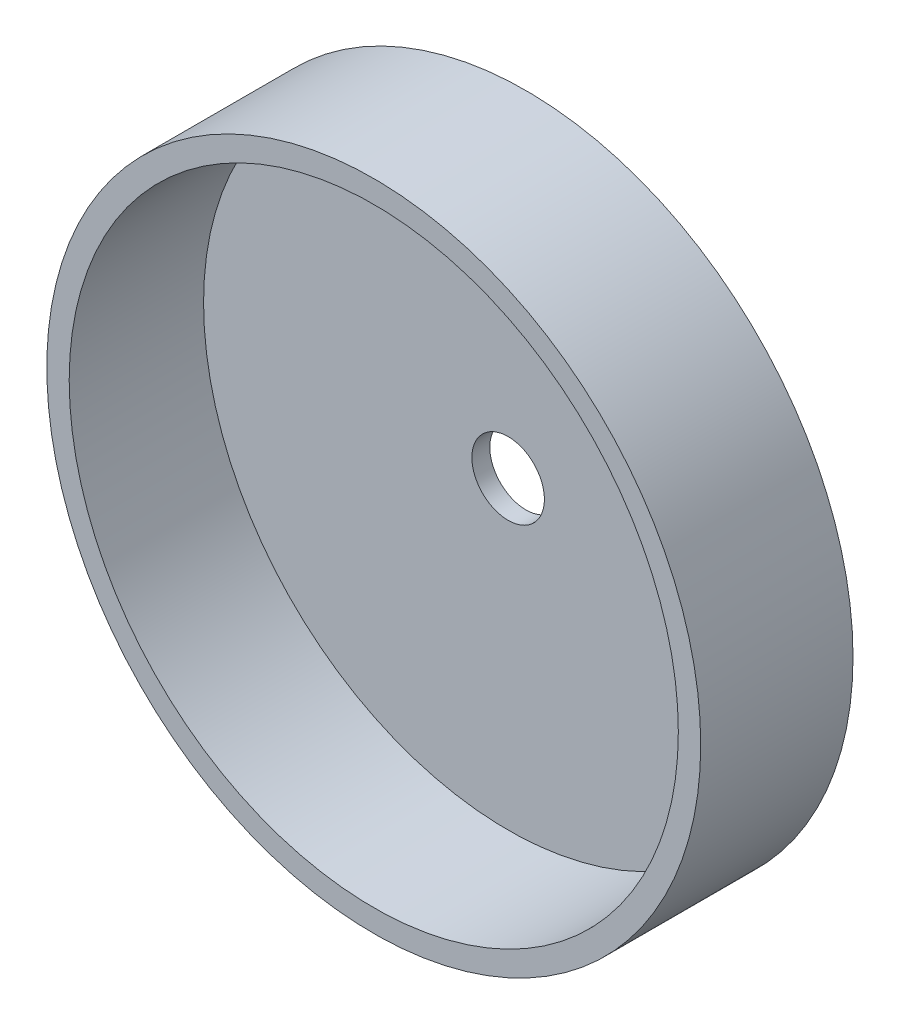
SolidWorks part; units mm, degrees
ref_plane "Plan de face" through (0, 0, 0) normal (0, 0, 1) x (1, 0, 0)
ref_plane "Plan de dessus" through (0, 0, 0) normal (0, 1, 0) x (1, 0, 0)
ref_plane "Plan de droite" through (0, 0, 0) normal (1, 0, 0) x (0, 0, -1)
sketch "Esquisse1" plane through (0, 0, 0) normal (0, 0, 1) x (1, 0, 0)
  circle A0 centre (0, 0) radius 34
  dimension "D1" = 68
extrude "Boss.-Extru.1" add sketch "Esquisse1" along normal blind 2
sketch "Esquisse2" plane through (0, 0, 2) normal (0, 0, 1) x (1, 0, 0)
  circle A0 centre (0, 0) radius 34
  circle A1 centre (0, 0) radius 36.5
  dimension "D1" = 68
  dimension "D2" = 2.5
extrude "Boss.-Extru.2" add sketch "Esquisse2" along normal blind 15 and the other way up to surface (2 mm away) other way up to face at (34, 0, 0)
sketch "Esquisse3" plane through (0, 0, 2) normal (0, 0, 1) x (1, 0, 0)
  circle A0 centre (0, 0) radius 4.05
  dimension "D1" = 8.1
extrude "Enlèv. mat.-Extru.1" cut sketch "Esquisse3" against normal through all both and the other way through all
